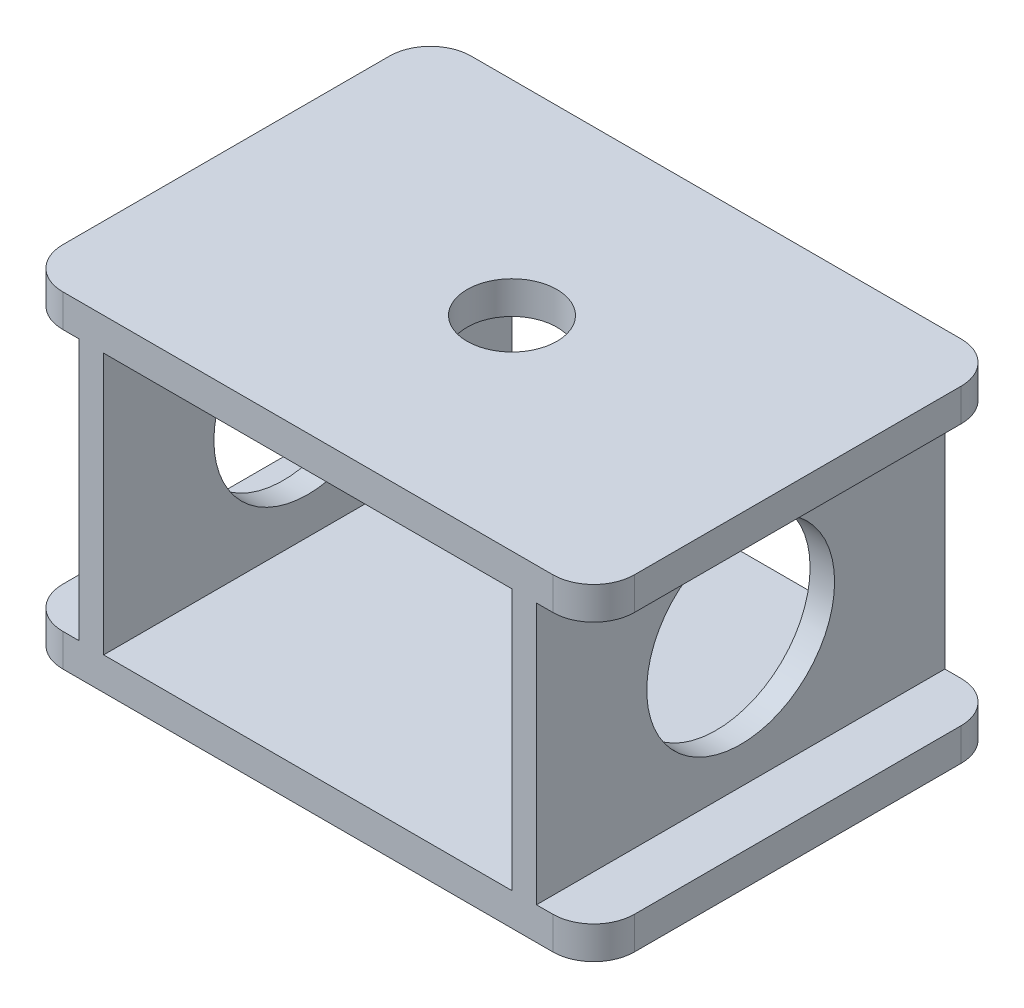
SolidWorks part; units mm, degrees
ref_plane "Front Plane" through (0, 0, 0) normal (0, 0, 1) x (1, 0, 0)
ref_plane "Top Plane" through (0, 0, 0) normal (0, 1, 0) x (1, 0, 0)
ref_plane "Right Plane" through (0, 0, 0) normal (1, 0, 0) x (0, 0, -1)
sketch "Sketch1" plane through (0, 0, 0) normal (0, 1, 0) x (1, 0, 0)
  line L1 (-30, 25) -> (30, 25)
  line L2 (-35, 20) -> (-35, -20)
  line L3 (-30, -25) -> (30, -25)
  line L4 (35, 20) -> (35, -20)
  line L5 (-35, 25) -> (35, -25) construction
  line L6 (-35, -25) -> (35, 25) construction
  arc A0 (30, -25) -> (35, -20) centre (30, -20) ccw
  arc A1 (-35, -20) -> (-30, -25) centre (-30, -20) ccw
  arc A2 (30, 25) -> (35, 20) centre (30, 20) cw
  arc A3 (-30, 25) -> (-35, 20) centre (-30, 20) ccw
  point P0 (0, 0)
  dimension "D3" = 5
  dimension "D1" = 50
  dimension "D2" = 70
extrude "Boss-Extrude1" add sketch "Sketch1" along normal blind 4
sketch "Sketch2" plane through (0, 4, 0) normal (0, 1, 0) x (1, 0, 0)
  line L0 (30, 25) -> (-30, 25) construction
  line L1 (-28, 25) -> (-25, 25)
  line L2 (-28, 25) -> (-28, -25)
  line L3 (-28, -25) -> (-25, -25)
  line L4 (-25, 25) -> (-25, -25)
  line L5 (-30, -25) -> (30, -25) construction
  line L6 (0, -19.8) -> (0, 19.8) construction
  line L7 (25, 25) -> (28, 25)
  line L8 (25, 25) -> (25, -25)
  line L9 (25, -25) -> (28, -25)
  line L10 (28, 25) -> (28, -25)
  dimension "D1" = 25
  dimension "D2" = 25
  dimension "D3" = 3
  dimension "D4" = 3
extrude "Boss-Extrude4" add sketch "Sketch2" along normal blind 32
sketch "Sketch4" plane through (0, 36, 0) normal (0, 1, 0) x (1, 0, 0)
  line L0 (-25, 25) -> (-28, 25) construction
  line L1 (-25, 25) -> (-28, 25)
  line L2 (28, 25) -> (25, 25) construction
  line L3 (28, 25) -> (25, 25)
  line L4 (-28, -25) -> (-28, 25)
  line L5 (-28, 25) -> (-30, 25)
  line L6 (-35, 20) -> (-35, -20)
  line L7 (-30, -25) -> (-28, -25)
  line L8 (-28, -25) -> (-28, 25)
  line L9 (-28, 25) -> (-30, 25)
  line L10 (-35, 20) -> (-35, -20)
  line L11 (-30, -25) -> (-28, -25)
  line L12 (-25, -25) -> (25, -25)
  line L13 (25, -25) -> (25, 25)
  line L14 (25, 25) -> (-25, 25)
  line L15 (-25, 25) -> (-25, -25)
  line L16 (-25, -25) -> (25, -25)
  line L17 (25, -25) -> (25, 25)
  line L18 (25, 25) -> (-25, 25)
  line L19 (-25, 25) -> (-25, -25)
  line L20 (30, 25) -> (28, 25)
  line L21 (28, 25) -> (28, -25)
  line L22 (28, -25) -> (30, -25)
  line L23 (35, -20) -> (35, 20)
  line L24 (30, 25) -> (28, 25)
  line L25 (28, 25) -> (28, -25)
  line L26 (28, -25) -> (30, -25)
  line L27 (35, -20) -> (35, 20)
  line L28 (-28, -25) -> (-25, -25) construction
  line L29 (-28, -25) -> (-25, -25)
  line L30 (25, -25) -> (28, -25) construction
  line L31 (25, -25) -> (28, -25)
  arc A2 (-30, 25) -> (-35, 20) centre (-30, 20) ccw
  arc A3 (-35, -20) -> (-30, -25) centre (-30, -20) ccw
  arc A4 (-30, 25) -> (-35, 20) centre (-30, 20) ccw
  arc A5 (-35, -20) -> (-30, -25) centre (-30, -20) ccw
  arc A6 (30, -25) -> (35, -20) centre (30, -20) ccw
  arc A7 (35, 20) -> (30, 25) centre (30, 20) ccw
  arc A8 (30, -25) -> (35, -20) centre (30, -20) ccw
  arc A9 (35, 20) -> (30, 25) centre (30, 20) ccw
  line M17 (-28, 25) -> (-28, -25)
  line M18 (-28, -25) -> (-25, -25)
  line M19 (-25, -25) -> (-25, 25)
  line M20 (-25, 25) -> (-28, 25)
  dimension "D1" = 0
  dimension "D2" = 0
  dimension "D3" = 0
extrude "Boss-Extrude5" add sketch "Sketch4" along normal blind 4 contours L17 L18 L16 M19 | L10 A5 L11 L9 A4 M17 | L27 A9 L24 L25 L26 A8 | L17 L31 L25 L3 | M20 M17 M18 M19
sketch "Sketch6" plane through (28, 0, 0) normal (1, 0, 0) x (0, 0, -1)
  line L0 (0, 22) -> (0, -22) construction
  line L1 (27.5, 0) -> (-27.5, 0) construction
  circle A0 centre (0, 20) radius 11.5
  dimension "D1" = 23
  dimension "D2" = 20
extrude "Cut-Extrude1" cut sketch "Sketch6" against normal blind 106
sketch "Sketch7" plane through (0, 40, 0) normal (0, 1, 0) x (1, 0, 0)
  circle A0 centre (0, 0) radius 5.5
  dimension "D1" = 11
extrude "Cut-Extrude2" cut sketch "Sketch7" against normal blind 10
